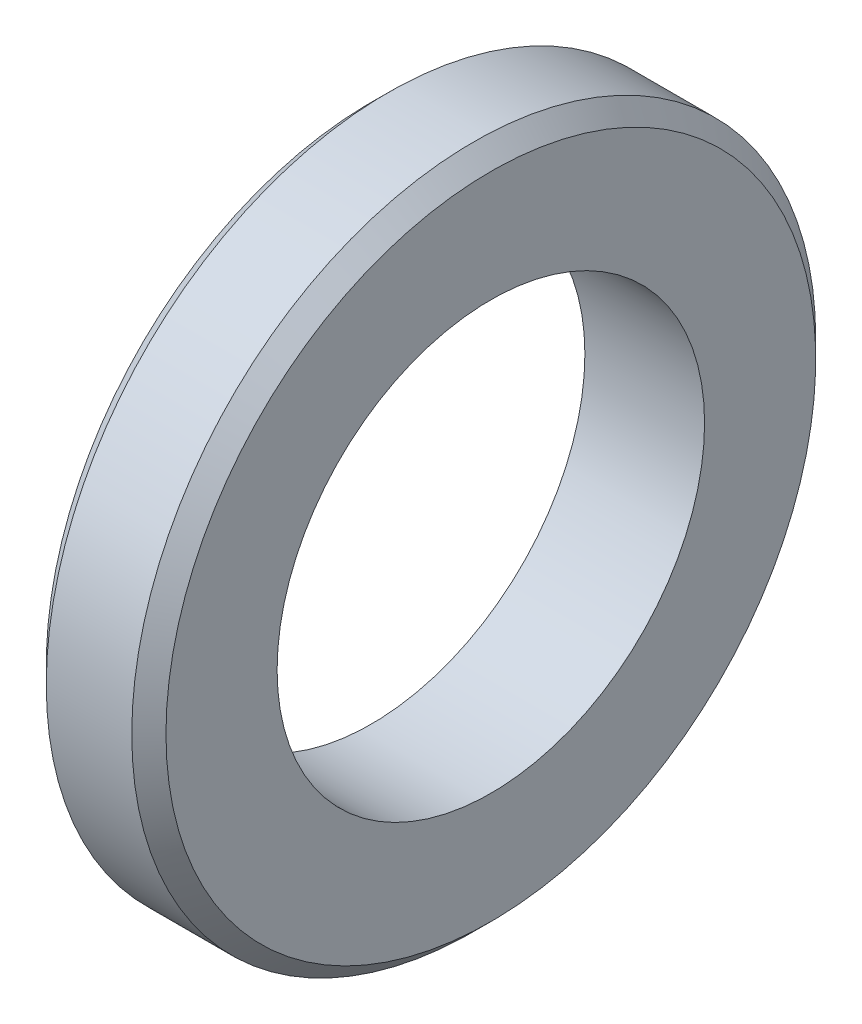
SolidWorks part; units mm, degrees
material "A5052S"
ref_plane "Front Plane" through (0, 0, 0) normal (0, 0, 1) x (1, 0, 0)
ref_plane "Top Plane" through (0, 0, 0) normal (0, 1, 0) x (1, 0, 0)
ref_plane "Right Plane" through (0, 0, 0) normal (1, 0, 0) x (0, 0, -1)
sketch "Sketch1" plane through (0, 0, 0) normal (0, 0, 1) x (1, 0, 0)
  line L0 (0, 0) -> (1.4, 0) construction
  line L1 (1.4, 2.5) -> (0, 2.5)
  line L2 (0, 2.5) -> (0, 4)
  line L4 (0, 4) -> (1.4, 4)
  line L6 (1.4, 4) -> (1.4, 2.5)
  dimension "D_s" = 5
  dimension "D" = 8
  dimension "L" = 1.4
revolve "Revolve1" add sketch "Sketch1" angle 360 about L0
chamfer "Chamfer1" distance 0.2 angle 45 2 edges at (0, 0, 4) (1.4, 0, 4)
equation "\"D1@Chamfer1\" = if ( \"L@Sketch1\" < 3 , 0.2 , 0.5 )"
